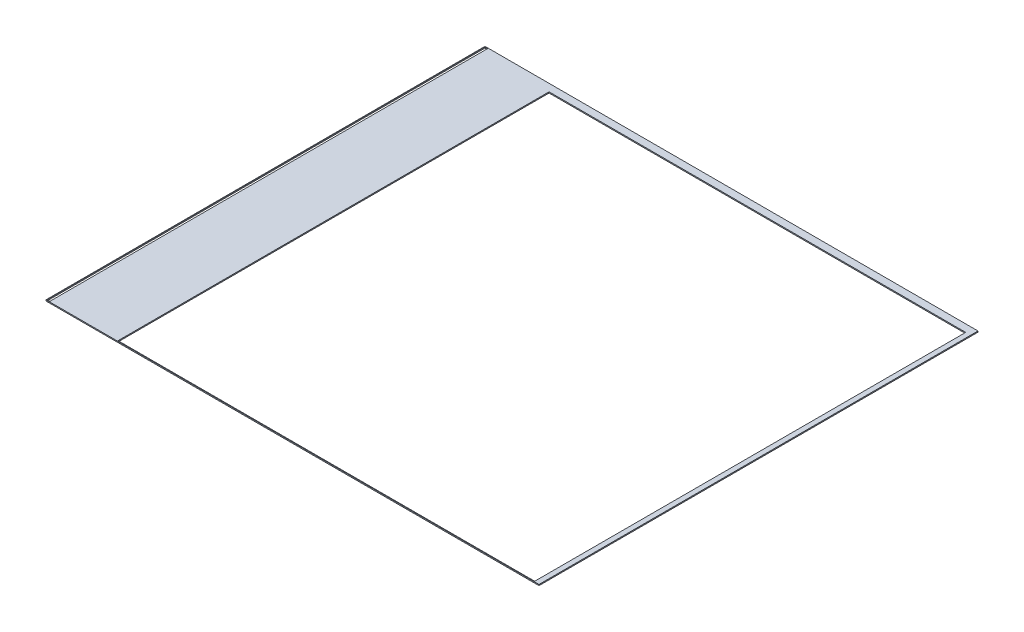
SolidWorks part; units mm, degrees
material "silicon D"
ref_plane "Front" through (0, 0, 0) normal (0, 0, 1) x (1, 0, 0)
ref_plane "Top" through (0, 0, 0) normal (0, 1, 0) x (1, 0, 0)
ref_plane "Right" through (0, 0, 0) normal (1, 0, 0) x (0, 0, -1)
sketch "Sketch1" plane through (0, 0, 0) normal (0, 1, 0) x (1, 0, 0)
  line L0 (11.355, 10.11) -> (-11.355, -10.11) construction
  line L1 (-11.355, 10.11) -> (11.355, 10.11) construction
  line L2 (-11.355, 10.11) -> (-11.355, -10.11) construction
  line L3 (-11.355, -10.11) -> (11.355, -10.11) construction
  line L4 (11.355, 10.11) -> (11.355, -10.11) construction
  line L5 (-11.365, 10.12) -> (11.365, 10.12)
  line L6 (11.365, 10.12) -> (11.365, -10.12)
  line L7 (-11.365, -10.12) -> (11.365, -10.12)
  line L8 (-11.365, 10.12) -> (-11.365, -10.12)
  point P4 (0, 0)
  dimension "D1" = 20.24
  dimension "D2" = 22.73
  dimension "D3" = 0.01
extrude "Extrude1" add sketch "Sketch1" along normal blind 0.05
sketch "Sketch2" plane through (0, 0, 0) normal (0, -1, 0) x (1, 0, 0)
  line L0 (-11.3446, 10.0882) -> (-11.2146, 10.0882) construction
  line L1 (-11.2146, -10.0968) -> (-11.3446, -10.0968) construction
  line L2 (-11.3446, -10.0968) -> (-11.3446, 10.0882) construction
  line L3 (-11.2146, 10.0882) -> (-11.2146, -10.0968) construction
  line L4 (-11.3446, 10.0882) -> (-11.2146, 10.0882)
  line L5 (-11.2146, -10.0968) -> (-11.3446, -10.0968)
  line L6 (-11.3446, -10.0968) -> (-11.3446, 10.0882)
  line L7 (-11.2146, 10.0882) -> (-11.2146, -10.0968)
extrude "Cut-Extrude1" cut sketch "Sketch2" against normal through all
sketch "Sketch3" plane through (0, 0, 0) normal (0, -1, 0) x (1, 0, 0)
  line L0 (-8.0718, 10.0914) -> (11.1378, 10.0914) construction
  line L1 (-8.0718, -9.7806) -> (-8.0718, 10.0914) construction
  line L2 (11.1378, 10.0914) -> (11.1378, -9.7806) construction
  line L3 (11.1378, -9.7806) -> (-8.0718, -9.7806) construction
  line L4 (-8.0718, 10.0914) -> (11.1378, 10.0914)
  line L5 (-8.0718, -9.7806) -> (-8.0718, 10.0914)
  line L6 (11.1378, 10.0914) -> (11.1378, -9.7806)
  line L7 (11.1378, -9.7806) -> (-8.0718, -9.7806)
extrude "Cut-Extrude2" cut sketch "Sketch3" against normal through all
